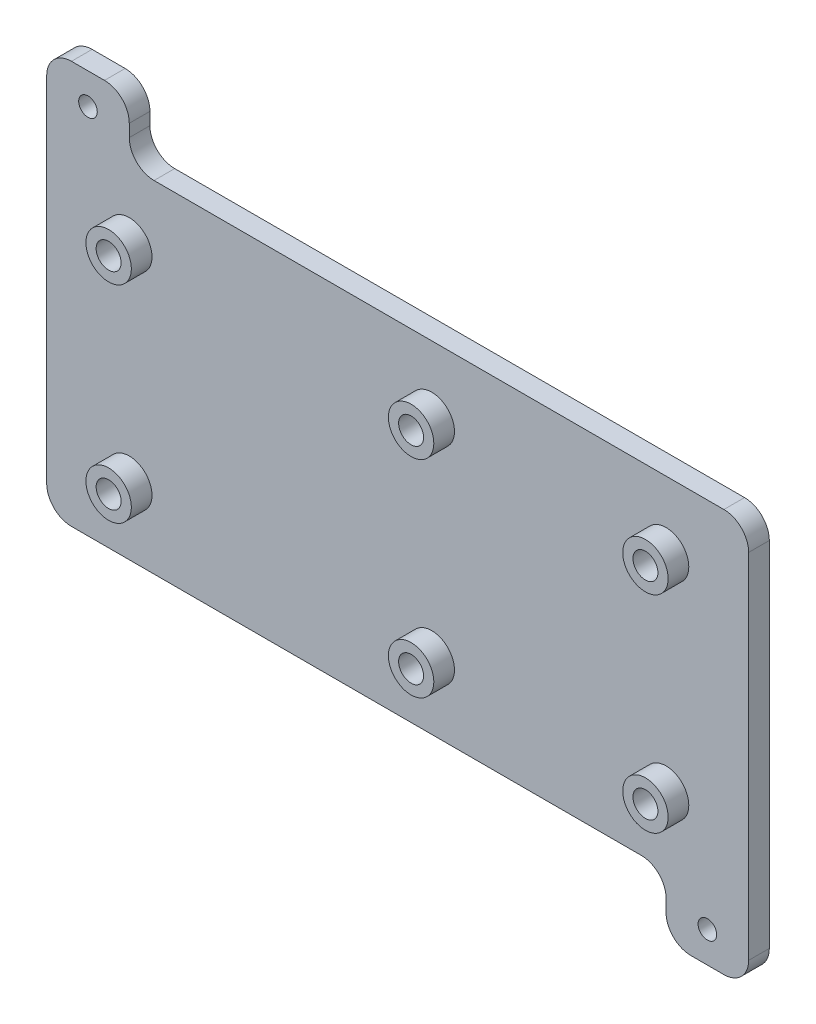
SolidWorks part; units mm, degrees
material "ABS"
ref_plane "X-Y Datum" through (0, 0, 0) normal (0, 0, 1) x (1, 0, 0)
ref_plane "X-Z Datum" through (0, 0, 0) normal (0, 1, 0) x (1, 0, 0)
ref_plane "Y-Z Datum" through (0, 0, 0) normal (1, 0, 0) x (0, 0, -1)
sketch "Sketch1" plane through (0, 0, 0) normal (0, 0, 1) x (1, 0, 0)
  line L1 (-70.0024, 29.9974) -> (70.0024, 29.9974) construction
  line L2 (-70.0024, 29.9974) -> (-70.0024, -29.9974) construction
  line L3 (-70.0024, -29.9974) -> (70.0024, -29.9974) construction
  line L4 (70.0024, 29.9974) -> (70.0024, -29.9974) construction
  line L5 (-70.0024, 29.9974) -> (70.0024, -29.9974) construction
  line L6 (-70.0024, -29.9974) -> (70.0024, 29.9974) construction
  line L7 (-85, 41.275) -> (85, 41.275)
  line L8 (-85, 41.275) -> (-85, -41.275)
  line L9 (-85, -41.275) -> (85, -41.275)
  line L10 (85, 41.275) -> (85, -41.275)
  line L11 (-85, 41.275) -> (85, -41.275) construction
  line L12 (-85, -41.275) -> (85, 41.275) construction
  point P0 (0, 0)
  point P6 (0, 0)
  dimension "D1" = 140.0048
  dimension "D2" = 59.9948
  dimension "D3" = 170
  dimension "D4" = 82.55
extrude "Boss-Extrude1" add sketch "Sketch1" along normal blind 5
sketch "Sketch2" plane through (0, 0, 5) normal (0, 0, 1) x (1, 0, 0)
  circle A0 centre (65, 25) radius 3.025
  circle A1 centre (65, -25) radius 3.025
  circle A2 centre (8.25, 25) radius 3.025
  circle A3 centre (8.25, -25) radius 3.025
  circle A4 centre (-65, 25) radius 3.025
  circle A5 centre (-65, -25) radius 3.025
  circle A6 centre (65, 25) radius 5.5
  circle A7 centre (8.25, 25) radius 5.5
  circle A8 centre (-65, 25) radius 5.5
  circle A9 centre (-65, -25) radius 5.5
  circle A10 centre (8.25, -25) radius 5.5
  circle A11 centre (65, -25) radius 5.5
  point P0 (65, -25)
  point P1 (65, 25)
  point P3 (8.25, 25)
  point P5 (8.25, -25)
  point P7 (-65, 25)
  point P9 (-65, -25)
  dimension "D1" = 6.05
  dimension "D2" = 11
extrude "Boss-Extrude2" add sketch "Sketch2" along normal blind 5
sketch "Sketch3" plane through (0, 0, 5) normal (0, 0, 1) x (1, 0, 0)
  line L0 (85, -41.275) -> (65, -56.275) construction
  line L1 (-85, 41.275) -> (-65, 41.275)
  line L2 (-85, 41.275) -> (-85, 56.275)
  line L3 (-85, 56.275) -> (-65, 56.275)
  line L4 (-65, 41.275) -> (-65, 56.275)
  line L5 (85, -41.275) -> (65, -41.275)
  line L6 (85, -41.275) -> (85, -56.275)
  line L7 (85, -56.275) -> (65, -56.275)
  line L8 (65, -41.275) -> (65, -56.275)
  line L9 (-65, 56.275) -> (-85, 41.275)
  point P10 (75, -48.775)
  point P11 (-75, 48.775)
  line M17 (85, 41.275) -> (-85, 41.275)
  line M19 (-85, -41.275) -> (85, -41.275)
  dimension "D1" = 15
  dimension "D2" = 20
  dimension "D3" = 15
  dimension "D4" = 20
extrude "Boss-Extrude3" add sketch "Sketch3" against normal blind 5 contours L9 L3 L2 | L4 L9 M17 | L0 L8 M19 | L6 L0 L7
fillet "Fillet1" radius 6 8 edges at (65, -41.275, 2.5) (65, -56.275, 2.5) (85, -56.275, 2.5) (85, 41.275, 2.5) (-65, 41.275, 2.5) (-65, 56.275, 2.5) (-85, 56.275, 2.5) (-85, -41.275, 2.5)
hole_wizard "M4 Clearance Hole1" positions "Sketch4" profile "Sketch5" hole size "M4" standard "ANSI Metric" end condition through all
sketch "Sketch4" plane through (0, 0, 5) normal (0, 0, 1) x (1, 0, 0)
  point P0 (-75, 48.775)
  point P3 (75, -48.775)
sketch "Sketch5" plane through (-75, 48.775, 5) normal (1, 0, 0) x (0, -1, 0)
  line L0 (0, 0) -> (0, 5)
  line L1 (0, 5) -> (2.25, 5)
  line L2 (2.25, 5) -> (2.25, 0)
  line L5 (2.25, 0) -> (0, 0)
  line L11 (0, -6.35) -> (0, 107.95) construction
  dimension "Thru Hole Dia." = 4.5
  dimension "Thru Hole Depth" = 5
